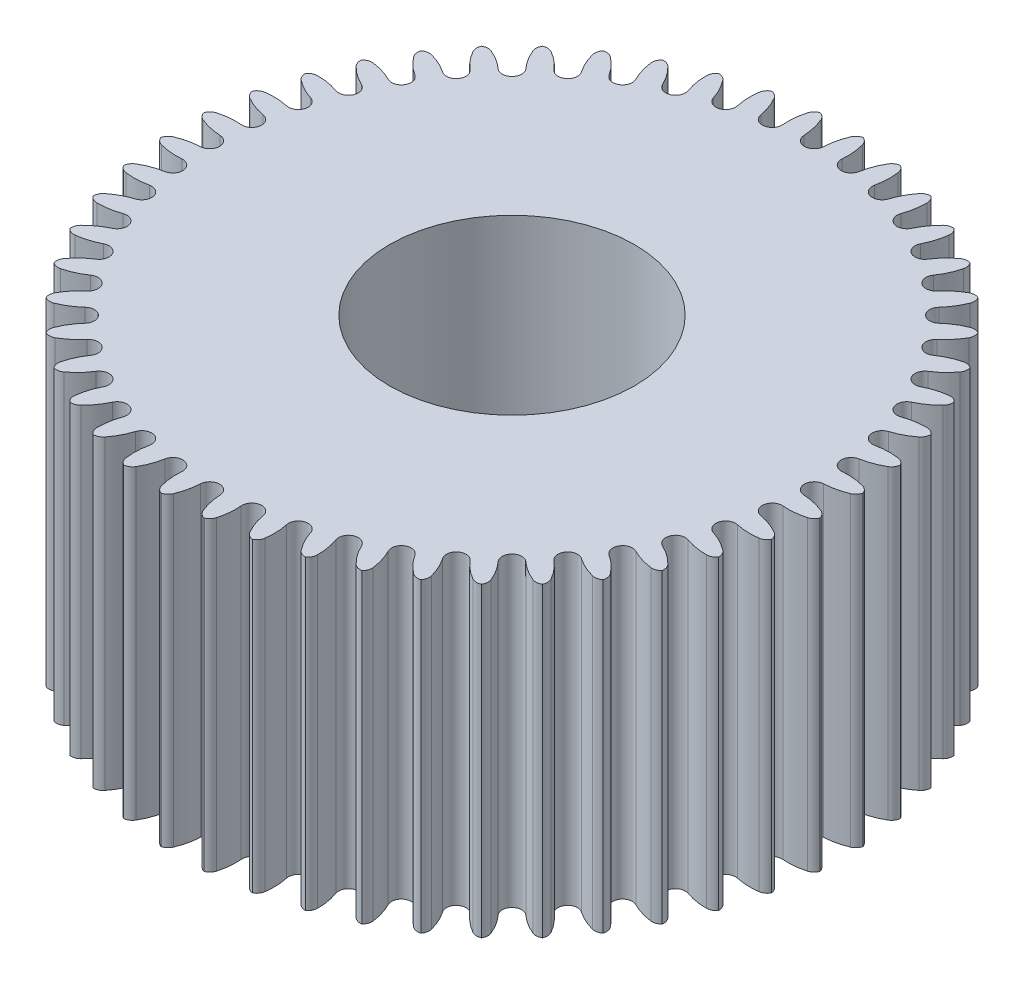
SolidWorks part; units mm, degrees
ref_plane "Front Plane" through (0, 0, 0) normal (0, 0, 1) x (1, 0, 0)
ref_plane "Top Plane" through (0, 0, 0) normal (0, 1, 0) x (1, 0, 0)
ref_plane "Right Plane" through (0, 0, 0) normal (1, 0, 0) x (0, 0, -1)
sketch "Sketch1" plane through (0, 0, 0) normal (0, 1, 0) x (1, 0, 0)
  circle A0 centre (0, 0) radius 27
  dimension "D1" = 54
extrude "Boss-Extrude1" add sketch "Sketch1" along normal blind 25
sketch "Sketch3" plane through (0, 0, 0) normal (0, -1, 0) x (1, 0, 0)
  line L0 (0, -24.6776) -> (0, -60.2569) construction
  arc A0 (0.7992, -24.6409) -> (-0.7992, -24.6409) centre (0, -24.6776) ccw
  arc A1 (0.7992, -24.6409) -> (1.2101, -26.4413) centre (5.9937, -24.4025) ccw
  circle A2 centre (1.946, -26.1276) radius 0.8
  circle A3 centre (0, 0) radius 27 construction
  circle A4 centre (-1.946, -26.1276) radius 0.8
  arc A5 (-0.7992, -24.6409) -> (-1.2101, -26.4413) centre (-5.9937, -24.4025) cw
  dimension "D1" = 1.6
  dimension "D2" = 10.4
  dimension "D3" = 1.45
  dimension "D4" = 1.6
  dimension "D5" = 3.892
extrude "Cut-Extrude1" cut sketch "Sketch3" against normal blind 25
pattern_circular "CirPattern1" count 48 over 360 about axis through (0, 0, 0) along (0, 1, 0) of "Cut-Extrude1"
sketch "Sketch4" plane through (0, 0, 0) normal (0, -1, 0) x (1, 0, 0)
  circle A0 centre (0, 0) radius 10
  dimension "D1" = 20
extrude "Cut-Extrude3" cut sketch "Sketch4" against normal blind 25
sketch "Croquis1" plane through (0, 0, 0) normal (0, -1, 0) x (1, 0, 0)
  line L0 (0, 0) -> (0, 23.8776) construction
  arc A0 (-0.7992, 24.6409) -> (0.7992, 24.6409) centre (0, 24.6776) ccw construction
